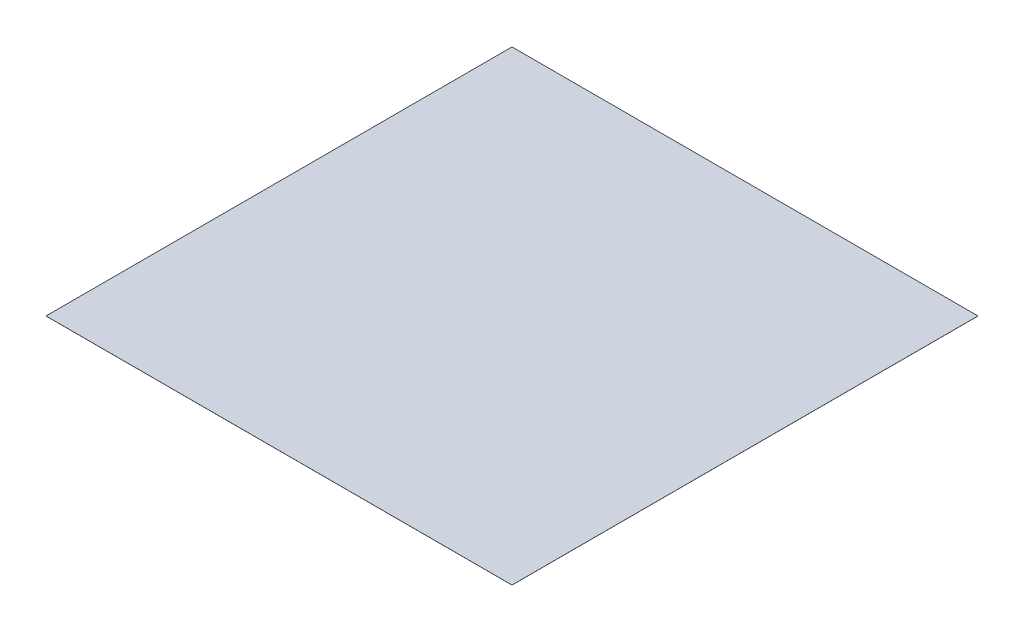
SolidWorks part; units mm, degrees
ref_plane "Front Plane" through (0, 0, 0) normal (0, 0, 1) x (1, 0, 0)
ref_plane "Top Plane" through (0, 0, 0) normal (0, 1, 0) x (1, 0, 0)
ref_plane "Right Plane" through (0, 0, 0) normal (1, 0, 0) x (0, 0, -1)
sketch "Sketch1" plane through (0, 0, 0) normal (0, 1, 0) x (1, 0, 0)
  line L1 (-1016, 1016) -> (1016, 1016)
  line L2 (-1016, 1016) -> (-1016, -1016)
  line L3 (-1016, -1016) -> (1016, -1016)
  line L4 (1016, 1016) -> (1016, -1016)
  line L5 (-1016, 1016) -> (1016, -1016) construction
  line L6 (-1016, -1016) -> (1016, 1016) construction
  point P0 (0, 0)
  dimension "D1" = 2032
  dimension "D2" = 2032
extrude "Boss-Extrude1" add sketch "Sketch1" along normal blind 0.254
